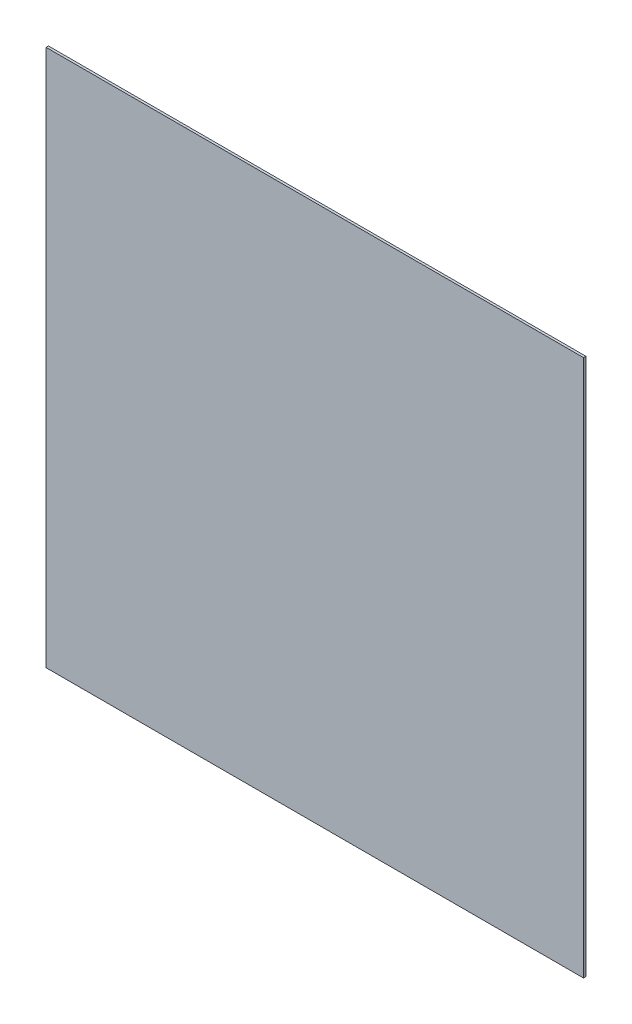
SolidWorks part; units mm, degrees
material "VITON"
ref_plane "Front Plane" through (0, 0, 0) normal (0, 0, 1) x (1, 0, 0)
ref_plane "Top Plane" through (0, 0, 0) normal (0, 1, 0) x (1, 0, 0)
ref_plane "Right Plane" through (0, 0, 0) normal (1, 0, 0) x (0, 0, -1)
sketch "Sketch1" plane through (0, 0, 0) normal (0, 0, 1) x (1, 0, 0)
  line L0 (150, 150) -> (-150, -150) construction
  line L1 (-150, 150) -> (150, 150)
  line L2 (-150, 150) -> (-150, -150)
  line L3 (-150, -150) -> (150, -150)
  line L4 (150, 150) -> (150, -150)
  dimension "D1" = 300
extrude "Boss-Extrude1" add sketch "Sketch1" along normal blind 1.325
